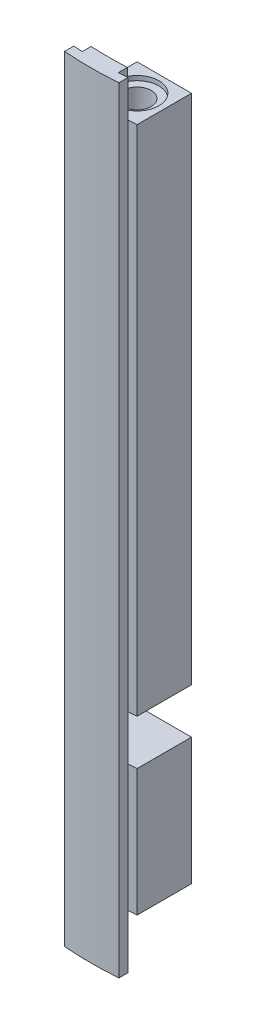
SolidWorks part; units mm, degrees
ref_plane "Front Plane" through (0, 0, 0) normal (0, 0, 1) x (1, 0, 0)
ref_plane "Top Plane" through (0, 0, 0) normal (0, 1, 0) x (1, 0, 0)
ref_plane "Right Plane" through (0, 0, 0) normal (1, 0, 0) x (0, 0, -1)
ref_plane "Plane7" through (0, -5, 0) normal (0, -1, 0) x (-1, 0, 0)
sketch "Sketch1" plane through (0, 0, 0) normal (0, 1, 0) x (1, 0, 0)
  circle A0 centre (0, 0) radius 37.5 construction
  dimension "D1" = 75
sketch "Sketch3" plane through (0, -5, 0) normal (0, -1, 0) x (1, 0, 0)
  line L0 (-3, 37.3798) -> (-3, 31.3798)
  line L1 (-3, 31.3798) -> (3, 31.3798)
  line L2 (3, 31.3798) -> (3, 37.3798)
  line L9 (0, 40.3758) -> (0, -39.6162) construction
  line L10 (0, -41.25) -> (0, 41.25) construction
  arc A0 (3, 37.3798) -> (-3, 37.3798) centre (0, 0) ccw
  circle A4 centre (0, 0) radius 37.5 construction
  point P19 (0, 0)
  dimension "D2" = 6
  dimension "D3" = 6
extrude "Boss-Extrude2" add sketch "Sketch3" along normal blind 75.5
sketch "Sketch5" plane through (0, 0, 0) normal (0, 1, 0) x (1, 0, 0)
  line L0 (-3, -38.3602) -> (-3, -39.3859)
  line L1 (3, -38.381) -> (3, -39.3859)
  line L2 (2, -38.4461) -> (2, -37.4466)
  line L3 (-2, -38.4253) -> (-2, -37.4466)
  line L12 (0, 40.7328) -> (0, -41.0085) construction
  line L13 (0, -41.25) -> (0, 41.25) construction
  arc A0 (-3, -39.3859) -> (3, -39.3859) centre (0, 0) ccw
  arc A1 (-2, -37.4466) -> (2, -37.4466) centre (0, 0) ccw
  arc A2 (3, -38.381) -> (2, -38.4461) centre (0, 0) cw
  arc A3 (-3, -38.3602) -> (-2, -38.4253) centre (0, 0) ccw
  circle A13 centre (0, 0) radius 37.5 construction
  point P33 (0, 0)
  dimension "D2" = 6
  dimension "D3" = 2
  dimension "D4" = 1.0049
  dimension "D5" = 1
extrude "Boss-Extrude3" add sketch "Sketch5" against normal blind 85.5
sketch "Sketch7" plane through (0, 0, 0) normal (1, 0, 0) x (0, 0, -1)
  line L0 (0, 41.25) -> (0, -41.25) construction
  line L1 (0, -61.5) -> (-37.5, -61.5)
  line L2 (0, -61.5) -> (0, -66.5)
  line L3 (0, -66.5) -> (-37.5, -66.5)
  line L4 (-37.5, -61.5) -> (-37.5, -66.5)
  line L6 (-31.3798, -80.5) -> (-37.3798, -80.5) construction
  line L7 (0, -27.0167) -> (0, -72.0117) construction
  dimension "D1" = 37.5
  dimension "D2" = 5
  dimension "D3" = 14
revolve "Cut-Revolve1" cut sketch "Sketch7" angle 360 about L7
ref_plane "Plane5" through (0, -80.5, 0) normal (0, -1, 0) x (-1, 0, 0)
sketch "Sketch9" plane through (0, -80.5, 0) normal (0, -1, 0) x (-1, 0, 0)
  line L0 (0, -31.1751) -> (0, -37.6667) construction
  line L1 (0, 42.35) -> (0, -42.35) construction
  line L2 (-3.1738, -34.4209) -> (3.1592, -34.4209) construction
  circle A0 centre (0, -34.4209) radius 1.55
  dimension "D2" = 3.1
extrude "Cut-Extrude4" cut sketch "Sketch9" against normal blind 4.3
sketch "Sketch10" plane through (0, -80.5, 0) normal (0, -1, 0) x (-1, 0, 0)
  line L0 (0, -31.1751) -> (0, -37.6667) construction
  line L2 (-3.1738, -34.4209) -> (3.1592, -34.4209) construction
  circle A0 centre (0, -34.4209) radius 2.4
  dimension "D2" = 4.8
extrude "Cut-Extrude5" cut sketch "Sketch10" against normal blind 0.5
sketch "Sketch12" plane through (0, -5, 0) normal (0, -1, 0) x (-1, 0, 0)
  circle A0 centre (0, 0) radius 37.5 construction
sketch "Sketch13" plane through (0, -5, 0) normal (0, -1, 0) x (-1, 0, 0)
  line L0 (0, -31.134) -> (0, -37.6256) construction
  line L1 (-2.6479, -34.3798) -> (2.8747, -34.3798) construction
  line L2 (3, -37.3798) -> (3, -31.3798) construction
  line L3 (-3, -31.3798) -> (-3, -37.3798) construction
  circle A0 centre (0, -34.3798) radius 2.4
  point P12 (2.8747, -34.3798)
sketch "Sketch14" plane through (0, -5, 0) normal (0, -1, 0) x (-1, 0, 0)
  line L0 (0, -31.134) -> (0, -37.6256) construction
  line L2 (-3.1738, -34.3798) -> (3.1592, -34.3798) construction
  line L3 (3, -37.3798) -> (3, -31.3798) construction
  line L4 (-3, -31.3798) -> (-3, -37.3798) construction
  circle A0 centre (0, -34.3798) radius 1.55
  dimension "D2" = 3.1
extrude "Cut-Extrude6" cut sketch "Sketch13" along normal blind 0.5
extrude "Cut-Extrude7" cut sketch "Sketch14" along normal blind 4.3
